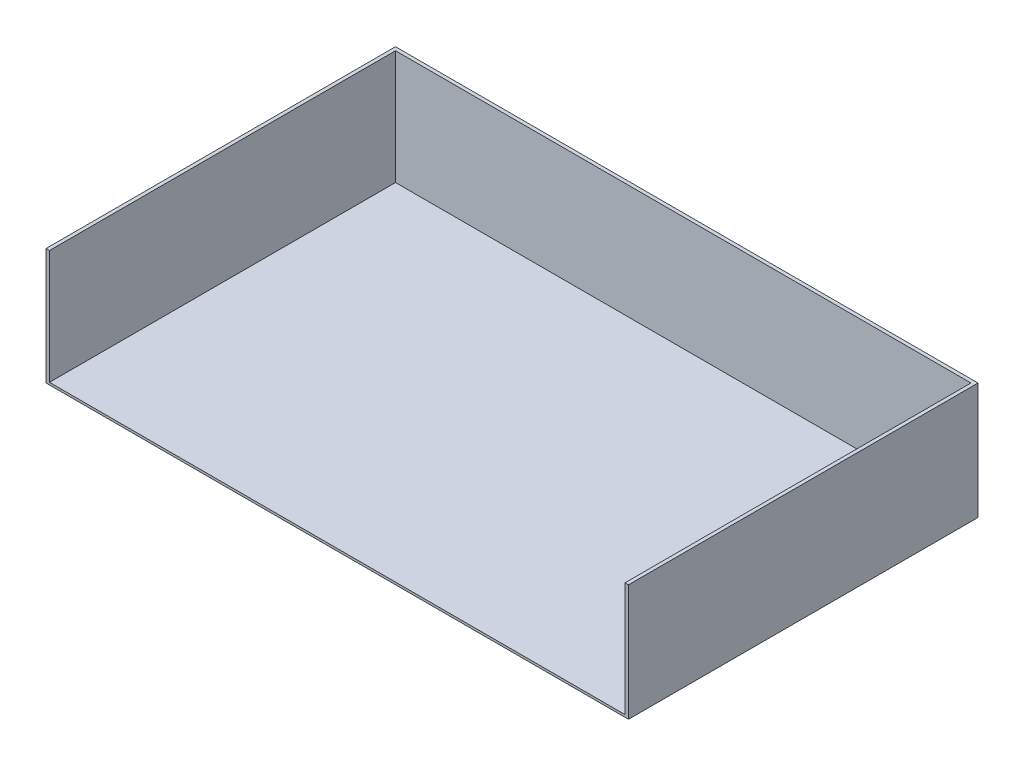
SolidWorks part; units mm, degrees
material "Acrylic (Medium-high impact)"
ref_plane "Front Plane" through (0, 0, 0) normal (0, 0, 1) x (1, 0, 0)
ref_plane "Top Plane" through (0, 0, 0) normal (0, 1, 0) x (1, 0, 0)
ref_plane "Right Plane" through (0, 0, 0) normal (1, 0, 0) x (0, 0, -1)
sketch "Sketch1" plane through (0, 0, 0) normal (0, 0, 1) x (1, 0, 0)
  line L1 (0, 0) -> (635, 0)
  line L2 (0, 0) -> (0, 127)
  line L3 (0, 127) -> (635, 127)
  line L4 (635, 0) -> (635, 127)
  dimension "D1" = 635
  dimension "D2" = 127
extrude "Boss-Extrude1" add sketch "Sketch1" along normal blind 381
sketch "Sketch2" plane through (0, 127, 0) normal (0, 1, 0) x (1, 0, 0)
  line L0 (3.81, -381) -> (3.81, -3.81)
  line L1 (635, -381) -> (0, -381) construction
  line L2 (3.81, -3.81) -> (631.19, -3.81)
  line L3 (631.19, -3.81) -> (631.19, -381)
  line L4 (631.19, -381) -> (3.81, -381)
  line L5 (635, 0) -> (0, 0) construction
  line L6 (635, -381) -> (635, 0) construction
  line L7 (0, -381) -> (0, 0) construction
  dimension "D1" = 3.81
  dimension "D2" = 3.81
  dimension "D3" = 3.81
extrude "Cut-Extrude1" cut sketch "Sketch2" against normal offset from surface (124.46 mm away) 2.54 up to face at (317.5, 0, 190.5)
equation "\"Wall Thickness\"= .15in"
equation "\"floor thickness\"= .10"
equation "\"D2@Sketch2\"=\"Wall Thickness\""
equation "\"D1@Sketch2\"=\"Wall Thickness\""
equation "\"D3@Sketch2\"=\"Wall Thickness\""
equation "\"D1@Cut-Extrude1\"=\"floor thickness\""
